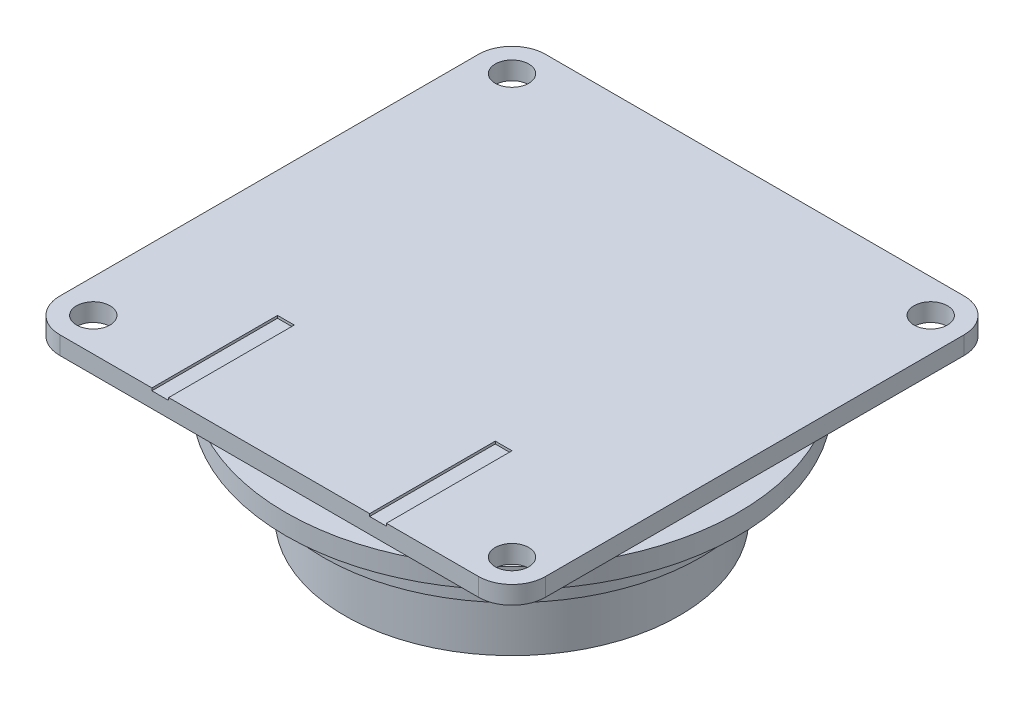
SolidWorks part; units mm, degrees
ref_plane "Front Plane" through (0, 0, 0) normal (0, 0, 1) x (1, 0, 0)
ref_plane "Top Plane" through (0, 0, 0) normal (0, 1, 0) x (1, 0, 0)
ref_plane "Right Plane" through (0, 0, 0) normal (1, 0, 0) x (0, 0, -1)
sketch "Sketch1" plane through (0, 0, 0) normal (0, 1, 0) x (1, 0, 0)
  circle A0 centre (0, 0) radius 20
  dimension "D1" = 40
extrude "Boss-Extrude1" add sketch "Sketch1" along normal blind 7.25
sketch "Sketch2" plane through (0, 7.25, 0) normal (0, 1, 0) x (1, 0, 0)
  circle A0 centre (0, 0) radius 22.5
  dimension "D1" = 45
extrude "Boss-Extrude2" add sketch "Sketch2" along normal blind 4.5
sketch "Sketch3" plane through (0, 11.75, 0) normal (0, 1, 0) x (1, 0, 0)
  circle A0 centre (0, 0) radius 27
  dimension "D1" = 54
extrude "Boss-Extrude3" add sketch "Sketch3" along normal blind 2.4
sketch "Sketch4" plane through (0, 14.15, 0) normal (0, 1, 0) x (1, 0, 0)
  line L0 (0, 0) -> (0, 40.4439) construction
  line L1 (4.484, 23.0682) -> (0, 0) construction
  circle A0 centre (4.484, 23.0682) radius 1
  circle A1 centre (0, 0) radius 22.5
  circle A2 centre (0, 0) radius 22.5
  circle A3 centre (22.2197, 7.6509) radius 1
  circle A4 centre (17.7357, -15.4174) radius 1
  circle A5 centre (-4.484, -23.0682) radius 1
  circle A6 centre (-22.2197, -7.6509) radius 1
  circle A7 centre (-17.7357, 15.4174) radius 1
  point P19 (0, 0)
  dimension "D2" = 2
  dimension "D3" = 11
  dimension "D4" = 6
  dimension "D1" = 0
extrude "Cut-Extrude1" cut sketch "Sketch4" against normal up to next contours A4 | A5 | A6 | A7 | A0 | A3
sketch "Sketch5" plane through (0, 14.15, 0) normal (0, 1, 0) x (1, 0, 0)
  circle A0 centre (0, 0) radius 23.5
  dimension "D1" = 47
extrude "Boss-Extrude4" add sketch "Sketch5" along normal blind 2.5 contours A0
sketch "Sketch6" plane through (0, 16.65, 0) normal (0, 1, 0) x (1, 0, 0)
  circle A0 centre (0, 0) radius 20.5
  dimension "D1" = 41
extrude "Boss-Extrude5" add sketch "Sketch6" along normal blind 1
sketch "Sketch7" plane through (0, 0, 0) normal (0, 0, 1) x (1, 0, 0)
  line L0 (20.5, 17.65) -> (20.5, 14.4)
  line L1 (20.5, 17.65) -> (17.25, 17.65)
  arc A0 (17.25, 17.65) -> (20.5, 14.4) centre (20.5, 17.65) ccw
sweep "Cut-Sweep1" cut profiles "Sketch7" path edge at (0, 17.65, 20.5)
sketch "Sketch8" plane through (0, 17.65, 0) normal (0, 1, 0) x (1, 0, 0)
  circle A0 centre (0, 0) radius 17.25
  dimension "D1" = 34.5
extrude "Boss-Extrude8" add sketch "Sketch8" along normal blind 1.25
sketch "Sketch10" plane through (0, 18.9, 0) normal (0, 1, 0) x (1, 0, 0)
  line L0 (0, 0) -> (29, 0) construction
  line L1 (-25, -29) -> (25, -29)
  line L2 (-29, -25) -> (-29, 25)
  line L3 (-25, 29) -> (25, 29)
  line L4 (29, -25) -> (29, 25)
  line L5 (-29, -29) -> (29, 29) construction
  line L6 (-29, 29) -> (29, -29) construction
  arc A0 (-25, -29) -> (-29, -25) centre (-25, -25) cw
  arc A1 (25, -29) -> (29, -25) centre (25, -25) ccw
  arc A2 (25, 29) -> (29, 25) centre (25, 25) cw
  arc A3 (-29, 25) -> (-25, 29) centre (-25, 25) cw
  circle A4 centre (-25, 25) radius 2
  circle A5 centre (25, 25) radius 2
  circle A6 centre (25, -25) radius 2
  circle A7 centre (-25, -25) radius 2
  point P0 (0, 0)
  dimension "D3" = 4
  dimension "D4" = 4
  dimension "D5" = 4
  dimension "D1" = 58
  dimension "D2" = 58
extrude "Boss-Extrude10" add sketch "Sketch10" along normal blind 2.15 contours A4 | A5 | A7 | A6 | A3 L2 A0 L1 A1 L4 A2 L3
sketch "Sketch11" plane through (0, 21.05, 0) normal (0, 1, 0) x (1, 0, 0)
  line L0 (0, -29) -> (0, 0) construction
  line L1 (-12, -29) -> (-14, -29)
  line L2 (-12, -29) -> (-12, -14)
  line L3 (-12, -14) -> (-14, -14)
  line L4 (25, 29) -> (-25, 29)
  line L5 (-29, 25) -> (-29, -25)
  line L6 (-25, -29) -> (25, -29)
  line L7 (29, -25) -> (29, 25)
  line L8 (25, 29) -> (-25, 29)
  line L9 (-29, 25) -> (-29, -25)
  line L10 (-25, -29) -> (25, -29)
  line L11 (29, -25) -> (29, 25)
  line L12 (-14, -29) -> (-14, -14)
  line L13 (12, -14) -> (14, -14)
  line L14 (14, -29) -> (14, -14)
  line L15 (12, -29) -> (14, -29)
  line L16 (12, -29) -> (12, -14)
  arc A4 (-25, 29) -> (-29, 25) centre (-25, 25) ccw
  arc A5 (-29, -25) -> (-25, -29) centre (-25, -25) ccw
  arc A6 (25, -29) -> (29, -25) centre (25, -25) ccw
  arc A7 (29, 25) -> (25, 29) centre (25, 25) ccw
  arc A8 (-25, 29) -> (-29, 25) centre (-25, 25) ccw
  arc A9 (-29, -25) -> (-25, -29) centre (-25, -25) ccw
  arc A10 (25, -29) -> (29, -25) centre (25, -25) ccw
  arc A11 (29, 25) -> (25, 29) centre (25, 25) ccw
  line M20 (-25, -29) -> (25, -29)
  dimension "D2" = 17
  dimension "D3" = 2
  dimension "D4" = 15
  dimension "D1" = 0
extrude "Cut-Extrude2" cut sketch "Sketch11" against normal blind 0.3 contours L12 L2 L3 M20 | L16 L10 L14 L13
